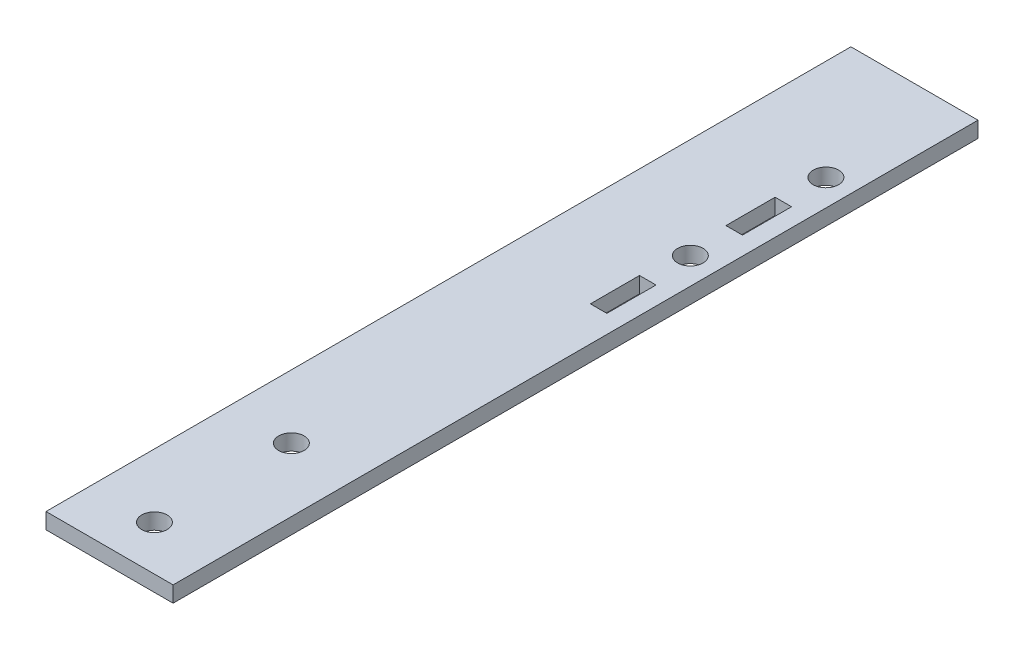
SolidWorks part; units mm, degrees
ref_plane "Front Plane" through (0, 0, 0) normal (0, 0, 1) x (1, 0, 0)
ref_plane "Top Plane" through (0, 0, 0) normal (0, 1, 0) x (1, 0, 0)
ref_plane "Right Plane" through (0, 0, 0) normal (1, 0, 0) x (0, 0, -1)
sketch "Sketch1" plane through (0, 0, 0) normal (0, 0, 1) x (1, 0, 0)
  line L0 (0, 0) -> (0, 2.3813)
  line L1 (0, 2.3813) -> (19.05, 2.3813)
  line L2 (19.05, 2.3813) -> (19.05, 0)
  line L3 (19.05, 0) -> (0, 0)
  dimension "D1" = 2.3813
  dimension "D2" = 19.05
extrude "Boss-Extrude1" add sketch "Sketch1" along normal blind 88.9
sketch "Sketch5" plane through (0, 2.3813, 0) normal (0, 1, 0) x (1, 0, 0)
  line L0 (16.6687, -25.2095) -> (19.05, -25.2095)
  line L2 (19.05, -88.9) -> (19.05, 0) construction
  line L10 (15.0813, -39.1478) -> (15.0813, -49.3078)
  line L11 (15.0813, -49.3078) -> (15.0813, -45.5295)
  line L17 (15.0813, -49.3078) -> (15.0813, -52.8955)
  line L24 (16.3176, -28.9877) -> (16.3176, -32.5755)
  line L25 (15.0813, -52.8955) -> (16.3176, -52.8955)
  line L26 (15.0813, -52.8955) -> (13.8449, -52.8955)
  line L27 (13.8449, -52.8955) -> (13.8449, -45.5295)
  line L28 (13.8449, -45.5295) -> (16.3176, -45.5295)
  line L29 (16.3176, -45.5295) -> (16.3176, -52.8955)
  line L30 (16.3176, -32.5755) -> (15.0813, -32.5755)
  line L31 (15.0813, -32.5755) -> (13.8449, -32.5755)
  line L32 (13.8449, -32.5755) -> (13.8449, -25.2095)
  line L33 (13.8449, -25.2095) -> (16.3176, -25.2095)
  line L34 (16.3176, -25.2095) -> (16.3176, -28.9877)
  circle A0 centre (15.0813, -39.1478) radius 1.905
  circle A3 centre (15.0813, -18.8277) radius 1.905
  dimension "D7" = 10.16
  dimension "D12" = 3.81
  dimension "D10" = 7.366
  dimension "D11" = 3.81
  dimension "D2" = 2.3813
  dimension "D3" = 3.5877
  dimension "D4" = 1.2363
  dimension "D5" = 1.2363
  dimension "D6" = 7.366
  dimension "D8" = 3.5878
  dimension "D9" = 1.2363
sketch "Sketch6" plane through (0, 2.3813, 0) normal (0, 1, 0) x (1, 0, 0)
sketch "Sketch7" plane through (0, 2.3813, 0) normal (0, 1, 0) x (1, 0, 0)
extrude "Cut-Extrude4" cut sketch "Sketch5" against normal through all
sketch "Sketch8" plane through (0, 2.3813, 0) normal (0, 1, 0) x (1, 0, 0)
  line L0 (0, -88.9) -> (0, -114.3)
  line L2 (19.05, -114.3) -> (19.05, -88.9)
  line L3 (0, -88.9) -> (19.05, -88.9)
  line L4 (0, -114.3) -> (0, -120.65)
  line L5 (0, -120.65) -> (19.05, -120.65)
  line L6 (19.05, -120.65) -> (19.05, -114.3)
  dimension "D1" = 25.4
  dimension "D2" = 6.35
sketch "Sketch9" plane through (0, 2.3813, 0) normal (0, 1, 0) x (1, 0, 0)
  line L0 (0, 0) -> (0, 29.6545)
  line L1 (0, 29.6545) -> (19.05, 29.6545)
  line L2 (19.05, 29.6545) -> (19.05, 0)
  line L3 (0, 0) -> (19.05, 0)
  dimension "D1" = 29.6545
extrude "Boss-Extrude4" add sketch "Sketch9" against normal blind 2.3813
sketch "Sketch10" plane through (0, 2.3813, 0) normal (0, 1, 0) x (1, 0, 0)
extrude "Boss-Extrude5" add sketch "Sketch8" against normal blind 2.3813
sketch "Sketch11" plane through (0, 2.3813, 0) normal (0, 1, 0) x (1, 0, 0)
  line L4 (9.525, -91.8083) -> (9.525, -115.824)
  circle A0 centre (9.525, -113.919) radius 1.905
  circle A2 centre (9.525, -93.3958) radius 1.905
  dimension "D2" = 3.81
  dimension "D3" = 24.0157
  dimension "D1" = 3.81
extrude "Cut-Extrude6" cut sketch "Sketch11" against normal blind 2.54
sketch "Sketch12" plane through (0, 2.3813, 0) normal (0, 1, 0) x (1, 0, 0)
  line L0 (0, 29.6545) -> (0, 0)
  line L1 (0, 0) -> (19.05, 0)
  line L2 (19.05, -120.65) -> (19.05, 29.6545) construction
  line L3 (19.05, 0) -> (19.05, 29.6545)
  line L4 (19.05, 29.6545) -> (0, 29.6545)
extrude "Cut-Extrude7" cut sketch "Sketch12" against normal through all
